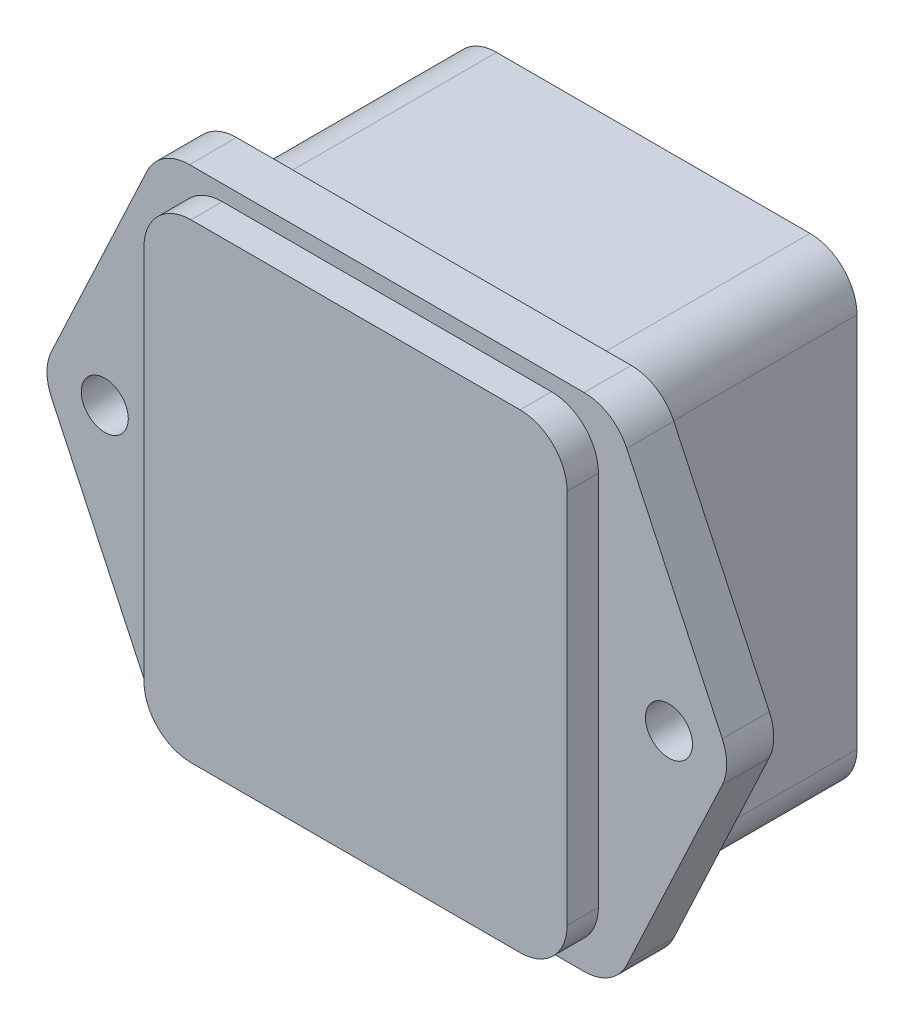
SolidWorks part; units mm, degrees
ref_plane "Front" through (0, 0, 0) normal (0, 0, 1) x (1, 0, 0)
ref_plane "Top" through (0, 0, 0) normal (0, 1, 0) x (1, 0, 0)
ref_plane "Right" through (0, 0, 0) normal (1, 0, 0) x (0, 0, -1)
sketch "Sketch1" plane through (0, 0, 0) normal (0, 0, 1) x (1, 0, 0)
  line L0 (-14.5, 16) -> (14.5, 16)
  line L3 (14.5, -16) -> (-14.5, -16)
  line L4 (-14.5, -16) -> (-22, 0)
  line L5 (-22, 0) -> (-14.5, 16)
  line L6 (14.5, 16) -> (22, 0)
  line L7 (22, 0) -> (14.5, -16)
  line L8 (-18, 0) -> (18, 0) construction
  circle A0 centre (-18, 0) radius 1.5
  circle A1 centre (18, 0) radius 1.5
  point P10 (0, 16)
  point P11 (0, -16)
  point P13 (0, 0)
  dimension "D4" = 3
  dimension "D1" = 29
  dimension "D2" = 32
  dimension "D3" = 44
  dimension "D5" = 36
extrude "Boss-Extrude1" add sketch "Sketch1" along normal blind 3
sketch "Sketch4" plane through (0, 0, 3) normal (0, 0, 1) x (1, 0, 0)
  line L1 (-13.5, 15) -> (13.5, 15)
  line L2 (-13.5, 15) -> (-13.5, -15)
  line L3 (-13.5, -15) -> (13.5, -15)
  line L4 (13.5, 15) -> (13.5, -15)
  line L5 (-13.5, 15) -> (13.5, -15) construction
  line L6 (-13.5, -15) -> (13.5, 15) construction
  point P0 (0, 0)
  dimension "D1" = 27
  dimension "D2" = 30
extrude "Boss-Extrude2" add sketch "Sketch4" along normal blind 2
sketch "Sketch5" plane through (0, 0, 0) normal (0, 0, -1) x (-1, 0, 0)
  line L1 (-13, -15) -> (13, -15)
  line L2 (-13, -15) -> (-13, 15)
  line L3 (-13, 15) -> (13, 15)
  line L4 (13, -15) -> (13, 15)
  line L5 (-13, -15) -> (13, 15) construction
  line L6 (-13, 15) -> (13, -15) construction
  point P0 (0, 0)
  dimension "D1" = 26
  dimension "D2" = 30
extrude "Boss-Extrude3" add sketch "Sketch5" along normal blind 14
fillet "Fillet1" radius 3 14 edges at (13, -15, -7) (13, 15, -7) (-13, 15, -7) (-13, -15, -7) (-14.5, -16, 1.5) (-22, 0, 1.5) (-14.5, 16, 1.5) (14.5, 16, 1.5) (14.5, -16, 1.5) (22, 0, 1.5) (13.5, -15, 4) (-13.5, -15, 4) (-13.5, 15, 4) (13.5, 15, 4)
